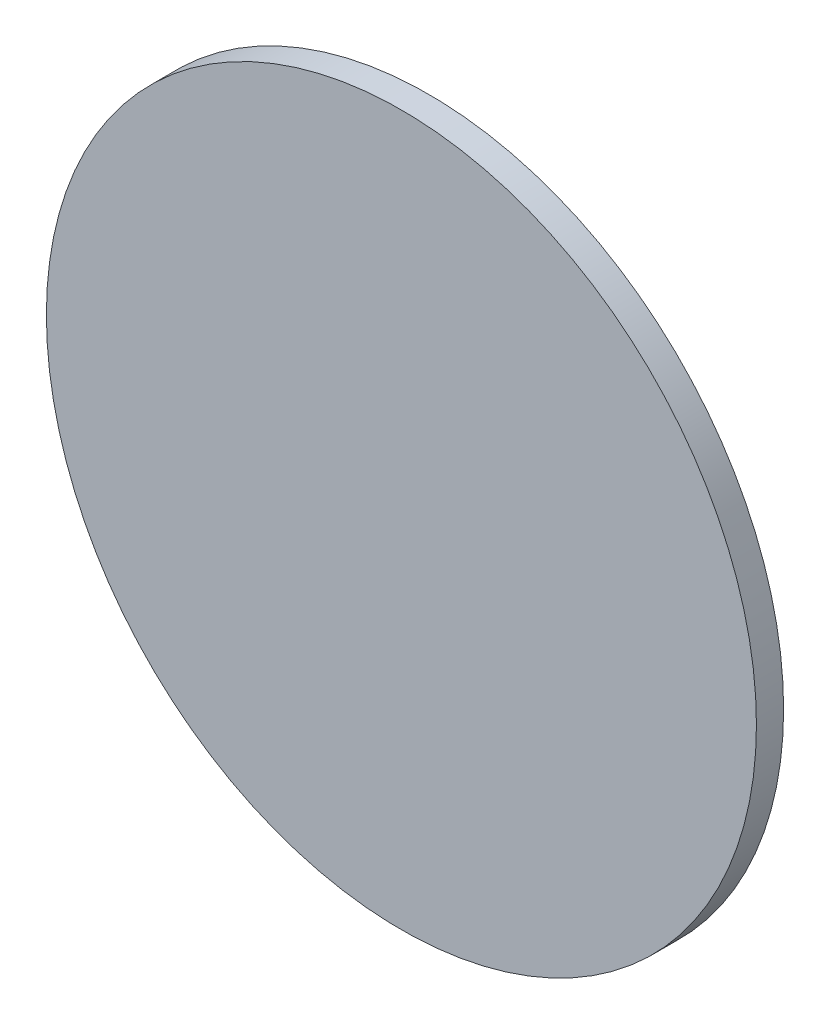
SolidWorks part; units mm, degrees
ref_plane "Piano frontale" through (0, 0, 0) normal (0, 0, 1) x (1, 0, 0)
ref_plane "Piano superiore" through (0, 0, 0) normal (0, 1, 0) x (1, 0, 0)
ref_plane "Piano destro" through (0, 0, 0) normal (1, 0, 0) x (0, 0, -1)
sketch "Schizzo1" plane through (0, 0, 0) normal (0, 0, 1) x (1, 0, 0)
  circle A0 centre (0, 0) radius 7.5
  dimension "D1" = 15
extrude "Estrusione-Estrusione1" add sketch "Schizzo1" along normal blind 0.574
